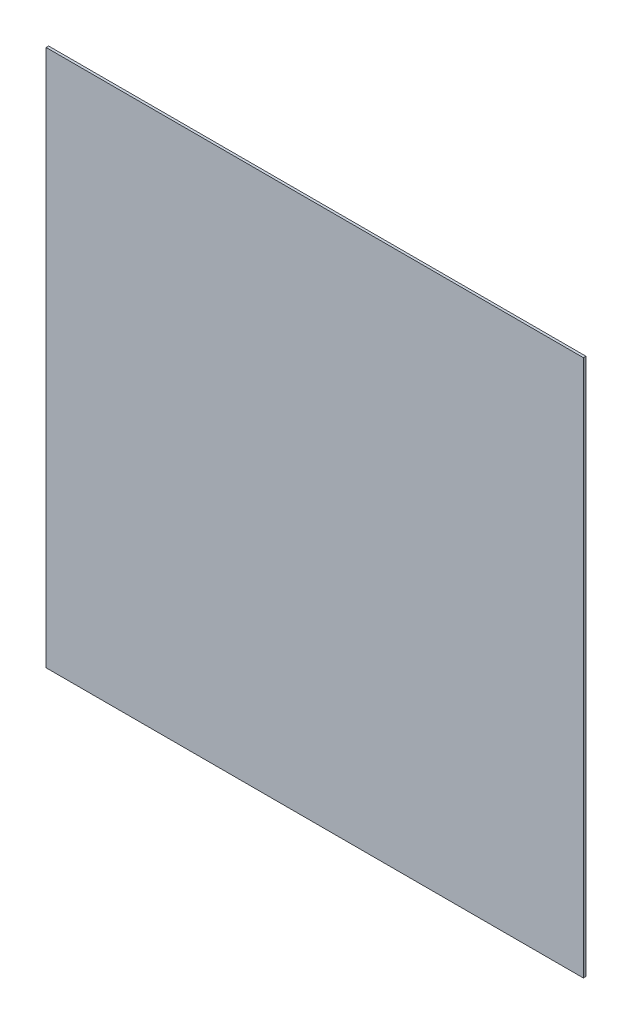
SolidWorks part; units mm, degrees
ref_plane "정면" through (0, 0, 0) normal (0, 0, 1) x (1, 0, 0)
ref_plane "윗면" through (0, 0, 0) normal (0, 1, 0) x (1, 0, 0)
ref_plane "우측면" through (0, 0, 0) normal (1, 0, 0) x (0, 0, -1)
sketch "스케치1" plane through (0, 0, 0) normal (0, 0, 1) x (1, 0, 0)
  line L1 (0, 0) -> (635, 0)
  line L2 (0, 0) -> (0, -635)
  line L3 (0, -635) -> (635, -635)
  line L4 (635, 0) -> (635, -635)
  dimension "D1" = 635
  dimension "D2" = 635
extrude "보스-돌출1" add sketch "스케치1" along normal blind 3
